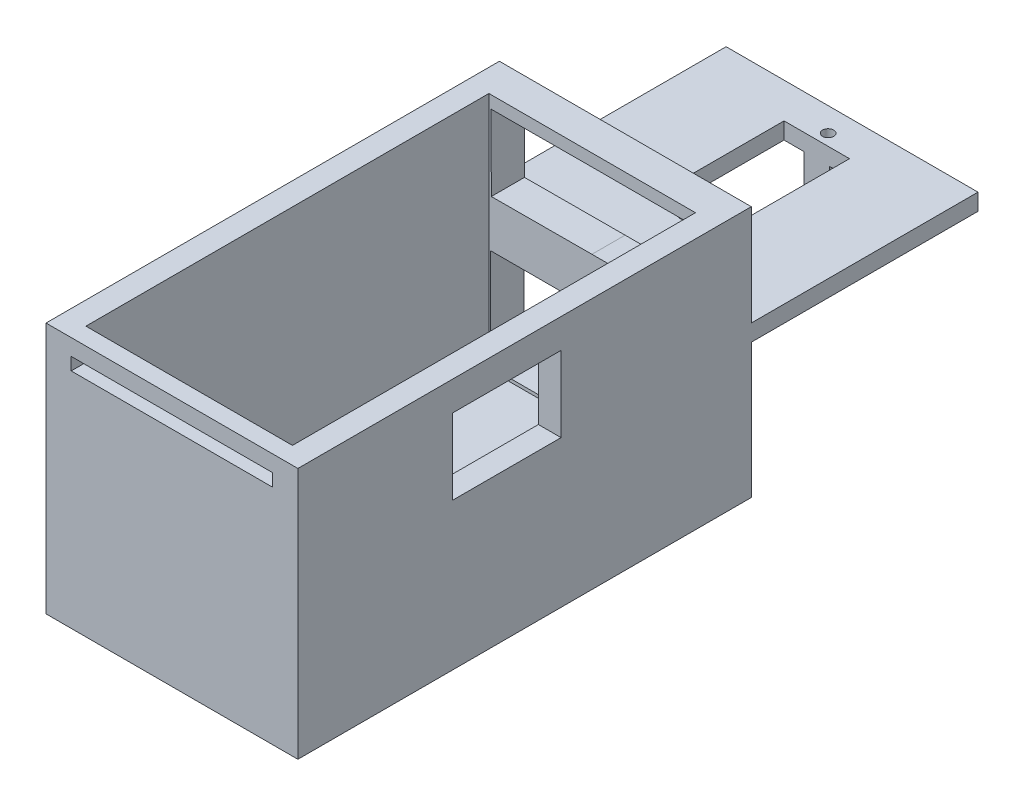
SolidWorks part; units mm, degrees
ref_plane "前基準面" through (0, 0, 0) normal (0, 0, 1) x (1, 0, 0)
ref_plane "上基準面" through (0, 0, 0) normal (0, 1, 0) x (1, 0, 0)
ref_plane "右基準面" through (0, 0, 0) normal (1, 0, 0) x (0, 0, -1)
sketch "草圖1" plane through (0, 0, 0) normal (0, 0, 1) x (1, 0, 0)
  line L0 (-3.6233, 55.0016) -> (-3.6233, -54.4404) construction
  line L1 (21.3767, 46.3024) -> (-28.6233, 46.3024)
  line L2 (-28.6233, 46.3024) -> (-28.6233, -3.6976)
  line L3 (-28.6233, -3.6976) -> (21.3767, -3.6976)
  line L4 (21.3767, 46.3024) -> (21.3767, -3.6976)
  point P7 (-3.6233, -3.6976)
  point P8 (-3.6233, 46.3024)
  dimension "D1" = 25
  dimension "D2" = 50
extrude "填料-伸長1" add sketch "草圖1" along normal blind 80 and the other way blind 55 contours L4 L3 L2 L1
sketch "草圖2" plane through (0, 46.3024, 0) normal (0, 1, 0) x (1, 0, 0)
  line L0 (-3.6233, -80) -> (-3.6233, 55) construction
  line L1 (21.3767, -80) -> (-28.6233, -80) construction
  line L2 (21.3767, 55) -> (-28.6233, 55) construction
  line L3 (16.8767, -76.5803) -> (-24.1233, -76.5803)
  line L4 (-24.1233, -76.5803) -> (-24.1233, 3.4197)
  line L5 (-24.1233, 3.4197) -> (16.8767, 3.4197)
  line L6 (16.8767, -76.5803) -> (16.8767, 3.4197)
  point P11 (-3.6233, -76.5803)
  point P12 (-3.6233, 3.4197)
  dimension "D1" = 80
  dimension "D2" = 20.5
extrude "除料-伸長1" cut sketch "草圖2" against normal blind 47.5
sketch "草圖3" plane through (0, 0, 0) normal (0, 1, 0) x (1, 0, 0)
  line L0 (-3.6233, 55) -> (-3.6233, -80) construction
  line L1 (21.3767, 55) -> (-28.6233, 55) construction
  line L2 (21.3767, -80) -> (-28.6233, -80) construction
  line L3 (-10.1233, 48) -> (2.8767, 48)
  line L4 (2.8767, 48) -> (2.8767, 24.5)
  line L5 (2.8767, 24.5) -> (-10.1233, 24.5)
  line L6 (-10.1233, 24.5) -> (-10.1233, 48)
  dimension "D1" = 13
  dimension "D2" = 6.5
  dimension "D3" = 23.5
  dimension "D4" = 7
extrude "除料-伸長2" cut sketch "草圖3" against normal blind 20 and the other way blind 60
sketch "草圖4" plane through (0, 0, 0) normal (0, 1, 0) x (1, 0, 0)
  line L7 (21.3767, 55) -> (21.3767, -80) construction
  line L8 (21.3767, 10) -> (21.3767, 55)
  line L9 (21.3767, 55) -> (-28.6233, 55)
  line L10 (-28.6233, 55) -> (-28.6233, 10)
  line L11 (-28.6233, 55) -> (-28.6233, -80) construction
  line L13 (-28.6233, 10) -> (21.3767, 10)
  dimension "D1" = 45
  dimension "D2" = 45
ref_plane "平面1" through (0, 46.3024, 0) normal (0, 1, 0) x (1, 0, 0)
sketch "草圖5" plane through (0, 46.3024, 0) normal (0, 1, 0) x (1, 0, 0)
  line L4 (21.3767, 55) -> (21.3767, -80) construction
  line L5 (-28.6233, 55) -> (21.3767, 55)
  line L6 (-28.6233, 55) -> (-28.6233, 10)
  line L7 (-28.6233, 10) -> (21.3767, 10)
  line L8 (21.3767, 55) -> (21.3767, 10)
  dimension "D1" = 45
extrude "除料-伸長4" cut sketch "草圖5" against normal blind 20
extrude "除料-伸長5" cut sketch "草圖4" against normal blind 10 and the other way blind 23 contours L8 L9 L10 L13
ref_plane "平面3" through (0, 0, -10) normal (0, 0, -1) x (-1, 0, 0)
sketch "草圖6" plane through (0, 0, -10) normal (0, 0, -1) x (-1, 0, 0)
  line L0 (3.6989, 47.2862) -> (3.6233, -3.6976) construction
  line L1 (28.6233, -3.6976) -> (-21.3767, -3.6976) construction
  line L2 (3.6938, 43.8846) -> (-16.3062, 43.8846)
  line L3 (-16.3062, 43.8846) -> (-16.3062, 28.8846)
  line L4 (-16.3062, 28.8846) -> (3.6716, 28.8846)
  line L5 (23.6493, 28.8253) -> (3.6716, 28.8846)
  line L6 (23.6938, 43.8253) -> (23.6493, 28.8253)
  line L7 (3.6938, 43.8846) -> (23.6938, 43.8253)
  dimension "D1" = 20
  dimension "D2" = 15
extrude "除料-伸長6" cut sketch "草圖6" against normal blind 10
sketch "草圖7" plane through (0, 0, -10) normal (0, 0, -1) x (-1, 0, 0)
  line L0 (3.6233, -3.6976) -> (3.6233, 46.3024) construction
  line L1 (28.6233, -3.6976) -> (-21.3767, -3.6976) construction
  line L2 (27.5, 46.3024) -> (-27.5, 46.3024) construction
  line L3 (-16.2313, 19.4395) -> (23.7687, 19.4395)
  line L4 (23.7687, 19.4395) -> (23.7687, -0.5605)
  line L5 (23.7687, -0.5605) -> (-16.2313, -0.5605)
  line L6 (-16.2313, 19.4395) -> (-16.2313, -0.5605)
  dimension "D1" = 20
  dimension "D2" = 40
extrude "除料-伸長7" cut sketch "草圖7" against normal blind 10
ref_plane "平面4" through (0, 0, 80) normal (0, 0, 1) x (1, 0, 0)
sketch "草圖9" plane through (0, 0, 80) normal (0, 0, 1) x (1, 0, 0)
  line L0 (-3.6233, 48.7853) -> (-3.6233, -3.6976) construction
  line L1 (-28.6233, -3.6976) -> (21.3767, -3.6976) construction
  line L2 (16.3767, 43.0664) -> (-23.6233, 43.0664)
  line L3 (-23.6233, 43.0664) -> (-23.6233, 40.5664)
  line L4 (-23.6233, 40.5664) -> (16.3767, 40.5664)
  line L5 (16.3767, 43.0664) -> (16.3767, 40.5664)
  point P9 (-3.6233, 40.5664)
  point P10 (-3.6233, 43.0664)
  dimension "D1" = 20
  dimension "D2" = 2.5
extrude "除料-伸長8" cut sketch "草圖9" against normal blind 10 contours L4 L5 L2 L3
ref_plane "平面5" through (0, 26.3024, 0) normal (0, 1, 0) x (1, 0, 0)
sketch "草圖11" plane through (0, 26.3024, 0) normal (0, 1, 0) x (1, 0, 0)
  line L0 (-3.6233, 24.5) -> (-3.6233, 40.5959) construction
  line L1 (-10.1233, 24.5) -> (2.8767, 24.5) construction
  line L2 (-10.1233, 36.25) -> (2.8767, 36.25) construction
  line L3 (-10.1233, 48) -> (-10.1233, 24.5) construction
  line L4 (2.8767, 24.5) -> (2.8767, 48) construction
  line L10 (-6.1233, 52.5) -> (-1.1233, 52.5)
  line L11 (-1.1233, 48) -> (-1.1233, 52.5)
  line L12 (-6.1233, 48) -> (-1.1233, 48)
  line L13 (-6.1233, 48) -> (-6.1233, 52.5)
  line L14 (-10.1233, 24.5) -> (2.8767, 24.5) construction
  line L15 (-6.1233, 24.5) -> (-1.1233, 24.5)
  line L16 (-6.1233, 24.5) -> (-6.1233, 19.5)
  line L17 (-6.1233, 19.5) -> (-1.1233, 19.5)
  line L18 (-1.1233, 24.5) -> (-1.1233, 19.5)
  dimension "D3" = 5
  dimension "D1" = 5
  dimension "D2" = 5
  dimension "D4" = 2.5
extrude "填料-伸長4" add sketch "草圖11" against normal blind 10
ref_plane "平面6" through (21.3767, 0, 0) normal (1, 0, 0) x (0, 0, -1)
sketch "草圖13" plane through (21.3767, 0, 0) normal (1, 0, 0) x (0, 0, -1)
  line L0 (-49.2632, 40.4831) -> (-49.2632, 25.4831)
  line L1 (-49.2632, 25.4831) -> (-27.7632, 25.4831)
  line L2 (-27.7632, 25.4831) -> (-27.7632, 40.4831)
  line L3 (-27.7632, 40.4831) -> (-49.2632, 40.4831)
  dimension "D1" = 21.5
  dimension "D2" = 15
extrude "除料-伸長10" cut sketch "草圖13" against normal blind 15
sketch "草圖14" plane through (0, 26.3024, 0) normal (0, 1, 0) x (1, 0, 0)
  line L0 (-6.1233, 50.25) -> (-1.1233, 50.25) construction
  line L1 (-6.1233, 48) -> (-6.1233, 52.5) construction
  line L2 (-1.1233, 48) -> (-1.1233, 52.5) construction
  line L3 (-3.6233, 52.5) -> (-3.6233, 19.5) construction
  line L4 (-6.1233, 52.5) -> (-1.1233, 52.5) construction
  line L5 (-6.1233, 19.5) -> (-1.1233, 19.5) construction
  line L6 (-6.1233, 22) -> (-1.1233, 22) construction
  line L7 (-6.1233, 24.5) -> (-6.1233, 19.5) construction
  line L8 (-1.1233, 24.5) -> (-1.1233, 19.5) construction
  circle A0 centre (-3.6233, 50.25) radius 1.1
  circle A1 centre (-3.6233, 22) radius 1.1
  dimension "D1" = 2.2
  dimension "D2" = 2.2
extrude "除料-伸長11" cut sketch "草圖14" against normal blind 12.4
